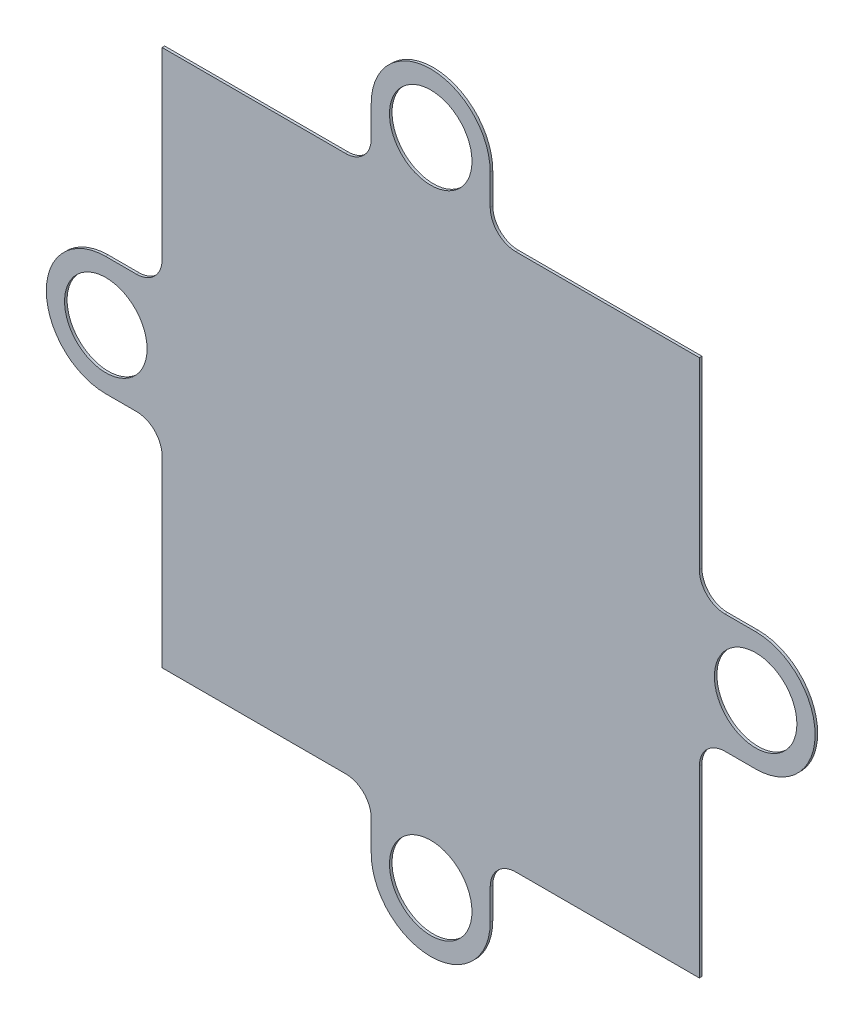
SolidWorks part; units mm, degrees
ref_plane "Front Plane" through (0, 0, 0) normal (0, 0, 1) x (1, 0, 0)
ref_plane "Top Plane" through (0, 0, 0) normal (0, 1, 0) x (1, 0, 0)
ref_plane "Right Plane" through (0, 0, 0) normal (1, 0, 0) x (0, 0, -1)
sketch "Sketch1" plane through (0, 0, 0) normal (0, 0, 1) x (1, 0, 0)
  line L0 (-4.65, 25.4) -> (-4.65, 23)
  line L1 (-21, -21) -> (-6.65, -21)
  line L2 (-21, -21) -> (-21, -6.65)
  line L3 (-21, 21) -> (-6.65, 21)
  line L4 (21, -21) -> (21, -6.65)
  line L5 (-21, -21) -> (21, 21) construction
  line L6 (-21, 21) -> (21, -21) construction
  line L7 (-6.65, 21) -> (-8.7591, 21)
  line L8 (4.65, 25.4) -> (4.65, 23)
  line L9 (6.65, 21) -> (7.1335, 21)
  line L10 (25.4, 4.65) -> (23, 4.65)
  line L11 (21, 6.65) -> (21, 8.7591)
  line L12 (25.4, -4.65) -> (23, -4.65)
  line L13 (21, -6.65) -> (21, -7.1335)
  line L14 (4.65, -25.4) -> (4.65, -23)
  line L15 (6.65, -21) -> (8.7591, -21)
  line L16 (-4.65, -25.4) -> (-4.65, -23)
  line L17 (-6.65, -21) -> (-7.1335, -21)
  line L18 (-25.4, -4.65) -> (-23, -4.65)
  line L19 (-21, -6.65) -> (-21, -8.7591)
  line L20 (-25.4, 4.65) -> (-23, 4.65)
  line L21 (-21, 6.65) -> (-21, 7.1335)
  line L22 (-21, 6.65) -> (-21, 21)
  line L23 (6.65, 21) -> (21, 21)
  line L24 (21, 6.65) -> (21, 21)
  line L25 (6.65, -21) -> (21, -21)
  circle A0 centre (0, 25.4) radius 3.225
  arc A1 (4.65, 25.4) -> (-4.65, 25.4) centre (0, 25.4) ccw
  arc A2 (4.65, 23) -> (6.65, 21) centre (6.65, 23) ccw
  arc A3 (-4.65, 23) -> (-6.65, 21) centre (-6.65, 23) cw
  circle A4 centre (25.4, 0) radius 3.225
  arc A5 (25.4, -4.65) -> (25.4, 4.65) centre (25.4, 0) ccw
  arc A6 (23, -4.65) -> (21, -6.65) centre (23, -6.65) ccw
  arc A7 (23, 4.65) -> (21, 6.65) centre (23, 6.65) cw
  circle A8 centre (0, -25.4) radius 3.225
  arc A9 (-4.65, -25.4) -> (4.65, -25.4) centre (0, -25.4) ccw
  arc A10 (-4.65, -23) -> (-6.65, -21) centre (-6.65, -23) ccw
  arc A11 (4.65, -23) -> (6.65, -21) centre (6.65, -23) cw
  circle A12 centre (-25.4, 0) radius 3.225
  arc A13 (-25.4, 4.65) -> (-25.4, -4.65) centre (-25.4, 0) ccw
  arc A14 (-23, 4.65) -> (-21, 6.65) centre (-23, 6.65) ccw
  arc A15 (-23, -4.65) -> (-21, -6.65) centre (-23, -6.65) cw
  point P0 (0, 0)
  point P53 (0, 0)
  dimension "D1" = 2
extrude "Boss-Extrude1" add sketch "Sketch1" along normal blind 0.2 contours L18 A15 L2 L1 A10 L16 A9 L14 A11 L15 L25 L4 A6 L12 A5 L10 A7 L11 L24 L23 L9 A2 L8 A1 L0 A3 L3 L22 L21 A14 L20 A13 A0 A4 A8 A12
